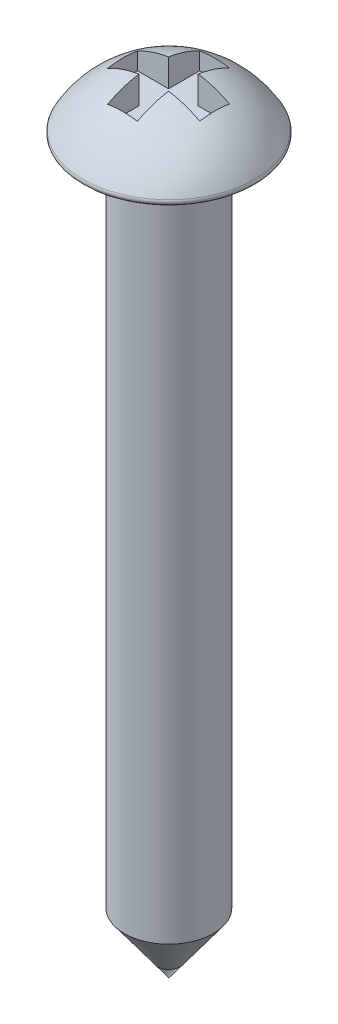
SolidWorks part; units mm, degrees
ref_plane "Plan de face" through (0, 0, 0) normal (0, 0, 1) x (1, 0, 0)
ref_plane "Plan de dessus" through (0, 0, 0) normal (0, 1, 0) x (1, 0, 0)
ref_plane "Plan de droite" through (0, 0, 0) normal (1, 0, 0) x (0, 0, -1)
sketch "Esquisse1" plane through (0, 0, 0) normal (0, 0, 1) x (1, 0, 0)
  line L0 (0, 3.8001) -> (0, -18) construction
  line L1 (2.2, 0) -> (1.1, 0)
  line L2 (1.1, 0) -> (1.1, -16.5)
  line L3 (1.1, -16.5) -> (0, -18)
  line L4 (0, -18) -> (0, 1.393)
  line L5 (-5.6455, -18) -> (12.232, -18) construction
  arc A0 (2.2, 0) -> (0, 1.393) centre (0, -1.0408) ccw
  dimension "D1" = 1.1
  dimension "D2" = 16.5
  dimension "D3" = 2.2
revolve "Révolution1" add sketch "Esquisse1" angle 360 about L0
fillet "Congé1" radius 0.1 1 edges at (-2.2, 0, 0)
ref_plane "Plan1" through (0, 1.1565, 0) normal (0, 1, 0) x (-1, 0, 0)
sketch "Esquisse2" plane through (0, 1.1565, 0) normal (0, 1, 0) x (-1, 0, 0)
  line L0 (0.0048, 1.1408) -> (0.0048, 0.0036) construction
  line L1 (-0.3619, 1.1408) -> (0.3716, 1.1408)
  line L2 (-0.3619, 1.1408) -> (-0.3619, 0.3704)
  line L3 (-0.3619, -1.1335) -> (0.3716, -1.1335)
  line L4 (0.3716, 1.1408) -> (0.3716, 0.3704)
  line L5 (-1.1323, 0.3704) -> (-0.3619, 0.3704)
  line L6 (-1.1323, 0.3704) -> (-1.1323, -0.3632)
  line L7 (-1.1323, -0.3632) -> (-0.3619, -0.3632)
  line L8 (1.142, 0.3704) -> (1.142, -0.3632)
  line L9 (0.0048, 0.0036) -> (0.0048, -1.1335) construction
  line L10 (1.142, 0.0036) -> (0.0048, 0.0036) construction
  line L11 (0.0048, 0.0036) -> (-1.1323, 0.0036) construction
  line L12 (0.3716, -0.3632) -> (1.142, -0.3632)
  line L13 (-0.3619, -0.3632) -> (-0.3619, -1.1335)
  line L14 (0.3716, 0.3704) -> (1.142, 0.3704)
  line L15 (0.3716, -0.3632) -> (0.3716, -1.1335)
extrude "Enlèv. mat.-Extru.1" cut sketch "Esquisse2" against normal mid plane 1
